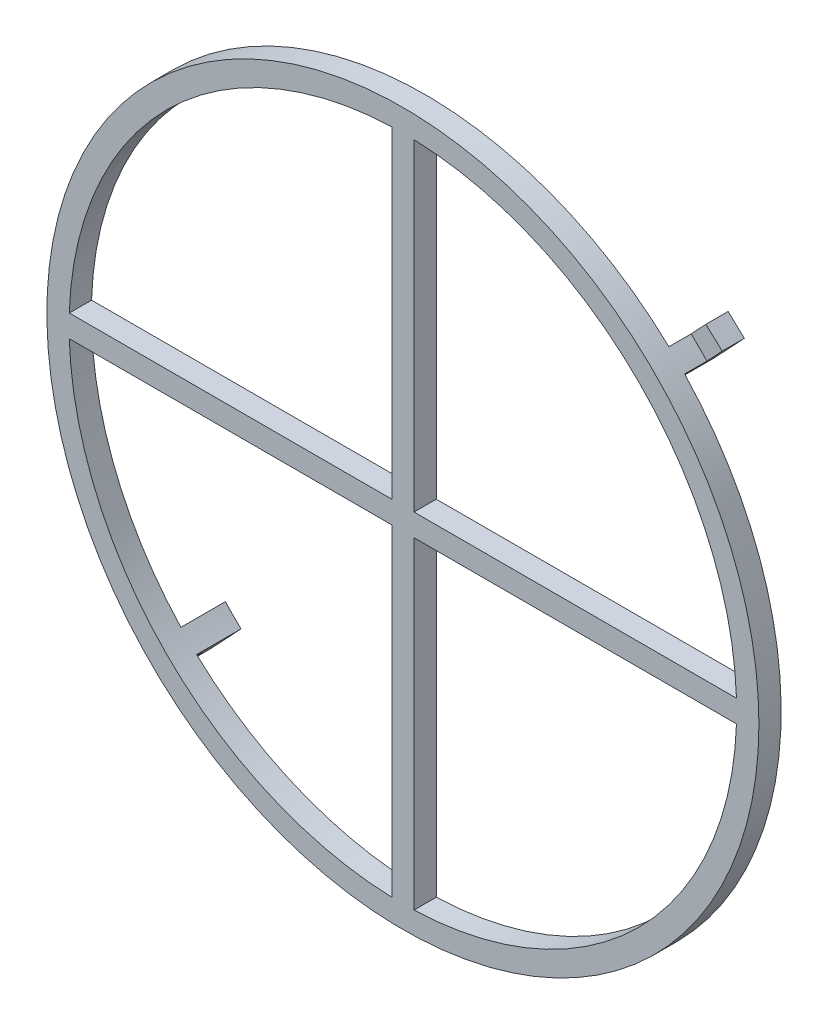
SolidWorks part; units mm, degrees
ref_plane "Front Plane" through (0, 0, 0) normal (0, 0, 1) x (1, 0, 0)
ref_plane "Top Plane" through (0, 0, 0) normal (0, 1, 0) x (1, 0, 0)
ref_plane "Right Plane" through (0, 0, 0) normal (1, 0, 0) x (0, 0, -1)
sketch "Sketch1" plane through (0, 0, 0) normal (0, 0, 1) x (1, 0, 0)
  line L0 (0, 15) -> (0, -15) construction
  line L1 (15, 0) -> (-15, 0) construction
  line L2 (-0.5, 14.9917) -> (-0.5, 0.5)
  line L3 (0.5, 14.9917) -> (0.5, 0.5)
  line L4 (-14.9917, 0.5) -> (-0.5, 0.5)
  line L5 (-14.9917, -0.5) -> (-0.5, -0.5)
  line L6 (0.5, 0.5) -> (14.9917, 0.5)
  line L7 (-0.5, -0.5) -> (-0.5, -14.9917)
  line L8 (0.5, -0.5) -> (14.9917, -0.5)
  line L9 (0.5, -0.5) -> (0.5, -14.9917)
  line L10 (13.9625, 13.9624) -> (-17.8573, -17.8574) construction
  line L11 (-12.766, 12.766) -> (14.8988, -14.8988) construction
  arc A0 (-14.9917, -0.5) -> (-0.5, -14.9917) centre (0, 0) ccw
  circle A1 centre (0, 0) radius 16
  arc A2 (14.9917, 0.5) -> (0.5, 14.9917) centre (0, 0) ccw
  arc A3 (-0.5, 14.9917) -> (-14.9917, 0.5) centre (0, 0) ccw
  arc A4 (0.5, -14.9917) -> (14.9917, -0.5) centre (0, 0) ccw
  dimension "D1" = 30
  dimension "D2" = 1
  dimension "D3" = 0.5
  dimension "D4" = 0.5
  dimension "D5" = 0.5
  dimension "D6" = 0.5
  dimension "D7" = 45
  dimension "D9" = 0.0001
  dimension "D10" = 45
sketch "Sketch2" plane through (0, 0, 0) normal (0, 0, 1) x (1, 0, 0)
  line L0 (13.9625, 13.9624) -> (-17.8573, -17.8574) construction
  line L1 (-12.766, 12.766) -> (14.8988, -14.8988) construction
  line L2 (0, -15) -> (0, 15) construction
  line L3 (-15, 0) -> (15, 0) construction
  line L4 (10.8654, 11.5724) -> (12.3744, 13.0814)
  line L5 (12.3744, 13.0814) -> (13.0815, 12.3743)
  line L6 (13.0815, 12.3743) -> (11.5725, 10.8653)
  circle A0 centre (0, 0) radius 15 construction
  circle A1 centre (0, 0) radius 15.8738 construction
  circle A2 centre (0, 0) radius 16 construction
  dimension "D1" = 0.5
  dimension "D2" = 0.5
  dimension "D3" = 18
extrude "Boss-Extrude1" add sketch "Sketch1" along normal blind 1
sketch "Sketch3" plane through (0, 0, 0) normal (0, 0, -1) x (-1, 0, 0)
  line L0 (-11.6618, 10.9546) -> (-10.9757, 10.2242)
  line L1 (-13.0815, 12.3743) -> (-11.5725, 10.8653) construction
  line L2 (-10.9547, 11.6617) -> (-10.27, 10.9328)
  line L3 (-10.8654, 11.5724) -> (-12.3744, 13.0814) construction
  line L4 (0, 0) -> (-12.313, 12.313) construction
  circle A0 centre (0, 0) radius 15 construction
  circle A1 centre (0, 0) radius 16
  arc A2 (-10.9547, 11.6617) -> (-11.6618, 10.9546) centre (0, 0) ccw
  arc A3 (-0.5, 14.9917) -> (-14.9917, 0.5) centre (0, 0) ccw construction
  arc A4 (-10.27, 10.9328) -> (-10.9757, 10.2242) centre (0, 0) ccw
  circle A5 centre (0, 0) radius 16 construction
  dimension "D1" = 0
extrude "Boss-Extrude2" add sketch "Sketch3" along normal blind 1
sketch "Sketch4" plane through (0, 0, -1) normal (0, 0, -1) x (-1, 0, 0)
  line L0 (-11.6618, 10.9546) -> (-10.9757, 10.2242) construction
  line L1 (-10.27, 10.9328) -> (-10.9547, 11.6617) construction
  line L2 (-11.6618, 10.9546) -> (-10.9757, 10.2242)
  line L3 (-10.27, 10.9328) -> (-10.9547, 11.6617)
  line L5 (-10.9547, 11.6617) -> (-11.6179, 12.3678)
  line L6 (-11.6618, 10.9546) -> (-12.3464, 11.6834)
  line L7 (-11.6179, 12.3678) -> (-12.3464, 11.6834)
  arc A0 (-10.27, 10.9328) -> (-10.9757, 10.2242) centre (0, 0) ccw construction
  arc A1 (-10.27, 10.9328) -> (-10.9757, 10.2242) centre (0, 0) ccw
  dimension "D1" = 1
extrude "Boss-Extrude3" add sketch "Sketch4" along normal blind 1
pattern_circular "CirPattern1" count 2 over 360 about axis through (0, 0, 0) along (0, 0, 1) of "Boss-Extrude2", "Boss-Extrude3"
